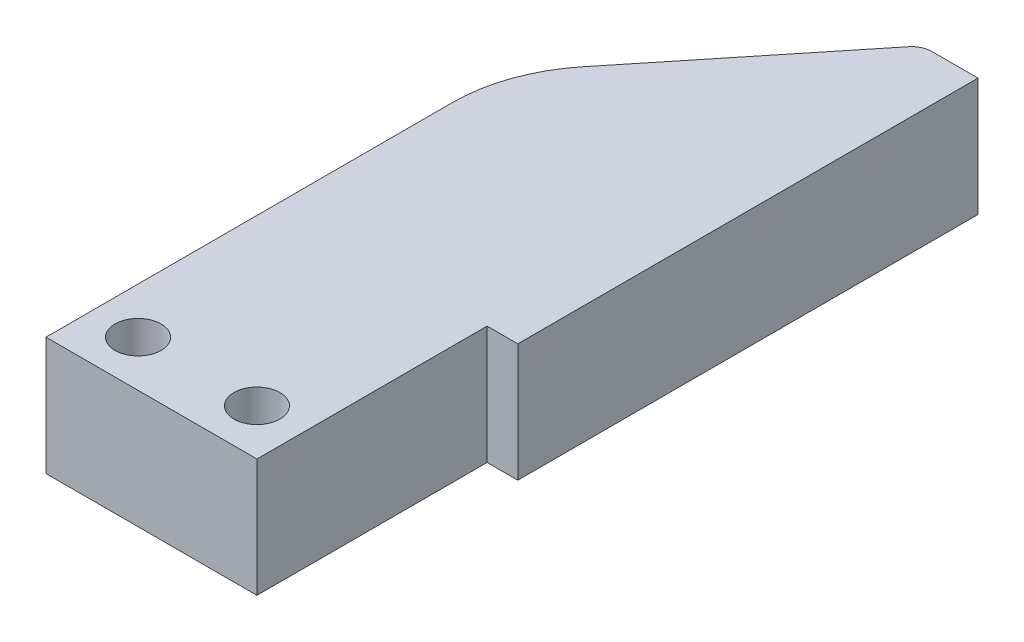
SolidWorks part; units mm, degrees
ref_plane "Front Plane" through (0, 0, 0) normal (0, 0, 1) x (1, 0, 0)
ref_plane "Top Plane" through (0, 0, 0) normal (0, 1, 0) x (1, 0, 0)
ref_plane "Right Plane" through (0, 0, 0) normal (1, 0, 0) x (0, 0, -1)
sketch "Sketch1" plane through (0, 0, 0) normal (0, 1, 0) x (1, 0, 0)
  line L0 (-13.75, -15) -> (0, -15)
  line L1 (-13.75, -15) -> (-13.75, 11.4669)
  line L6 (-6.875, -18.3439) -> (-6.875, -15) construction
  line L7 (0, 0) -> (0, -15)
  line L8 (-11.5305, 17.7489) -> (-2.0401, 29.503)
  line L11 (2, 30) -> (2, 0)
  line L12 (2, 0) -> (0, 0)
  line L13 (-1, 30) -> (2, 30)
  arc A1 (-2.0401, 29.503) -> (-1, 30) centre (-1, 28.6632) cw
  circle A3 centre (-10.75, -12) radius 1.5
  circle A5 centre (-3, -12) radius 1.5
  arc A6 (-13.75, 11.4669) -> (-11.5305, 17.7489) centre (-3.75, 11.4669) cw
  point P15 (-13.75, 15)
  dimension "D2" = 3
  dimension "D6" = 1.3368
  dimension "D10" = 3
  dimension "D12" = 3
  dimension "D13" = 10
  dimension "D3" = 13.75
  dimension "D4" = 18.6403
  dimension "D5" = 30
  dimension "D7" = 30
  dimension "D8" = 15
  dimension "D9" = 2
  dimension "D11" = 3
  dimension "D14" = 7.75
extrude "Boss-Extrude3" add sketch "Sketch1" along normal mid plane 7.7
